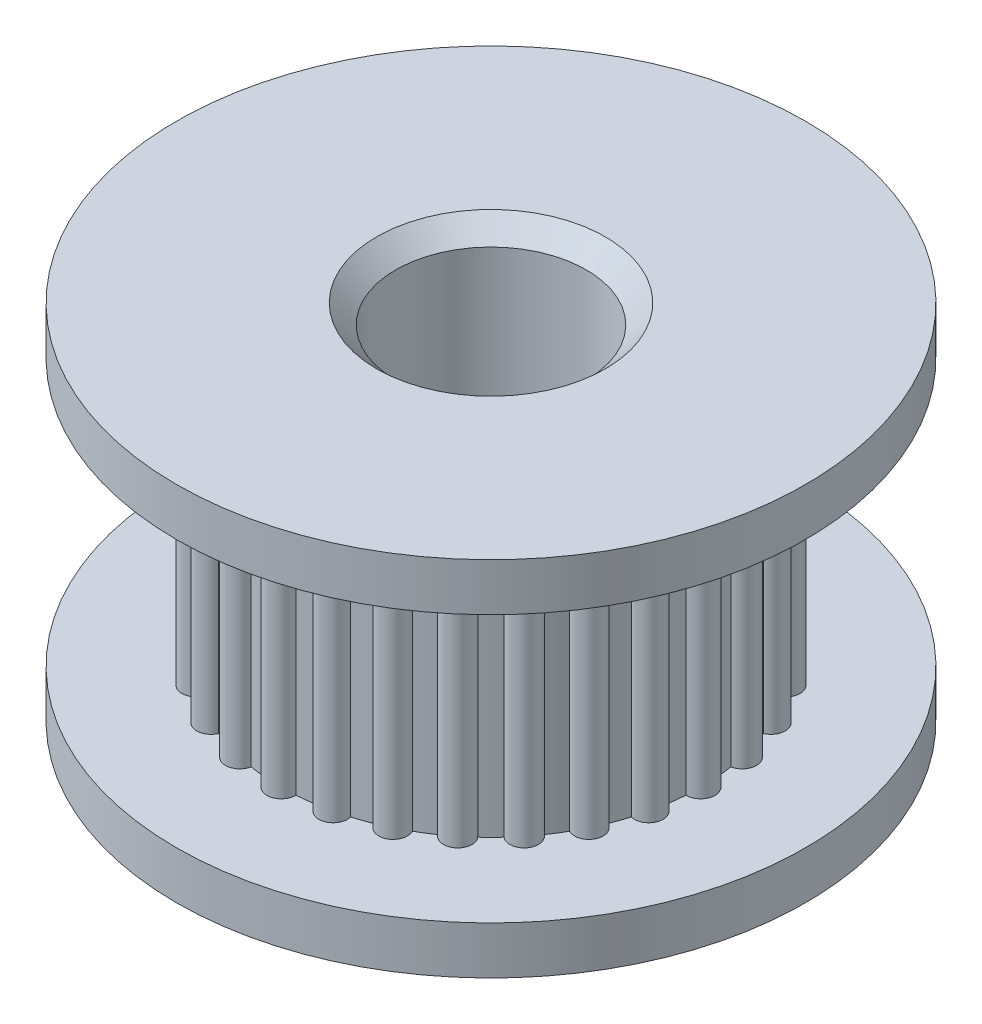
SolidWorks part; units mm, degrees
ref_plane "Front Plane" through (0, 0, 0) normal (0, 0, 1) x (1, 0, 0)
ref_plane "Top Plane" through (0, 0, 0) normal (0, 1, 0) x (1, 0, 0)
ref_plane "Right Plane" through (0, 0, 0) normal (1, 0, 0) x (0, 0, -1)
sketch "Sketch1" plane through (0, 0, 0) normal (0, 1, 0) x (1, 0, 0)
  circle A0 centre (0, 0) radius 8.382
  dimension "D1" = 16.764
extrude "Boss-Extrude1" add sketch "Sketch1" against normal blind 1.27
sketch "Sketch2" plane through (0, 0, 0) normal (0, 1, 0) x (1, 0, 0)
  circle A0 centre (0, 0) radius 5.969 construction
  circle A1 centre (0, 0) radius 5.588 construction
  arc A2 (-5.575, -0.3808) -> (-5.575, 0.3808) centre (-5.588, 0) cw
  circle A3 centre (0, 0) radius 5.588 construction
  arc A4 (-5.52, 0.8693) -> (-5.3505, 1.6118) centre (-5.4479, 1.2434) cw
  arc A6 (-5.1881, 2.0758) -> (-4.8577, 2.762) centre (-5.0346, 2.4245) cw
  arc A8 (-4.5961, 3.1783) -> (-4.1213, 3.7737) centre (-4.3689, 3.4841) cw
  arc A10 (-3.7737, 4.1213) -> (-3.1783, 4.5961) centre (-3.4841, 4.3689) cw
  arc A12 (-2.762, 4.8577) -> (-2.0758, 5.1881) centre (-2.4245, 5.0346) cw
  arc A14 (-1.6118, 5.3505) -> (-0.8693, 5.52) centre (-1.2434, 5.4479) cw
  arc A16 (-0.3808, 5.575) -> (0.3808, 5.575) centre (0, 5.588) cw
  circle A17 centre (0, 0) radius 5.588
  arc A18 (0.8693, 5.52) -> (1.6118, 5.3505) centre (1.2434, 5.4479) cw
  circle A19 centre (0, 0) radius 5.588
  arc A20 (2.0758, 5.1881) -> (2.762, 4.8577) centre (2.4245, 5.0346) cw
  circle A21 centre (0, 0) radius 5.588
  arc A22 (3.1783, 4.5961) -> (3.7737, 4.1213) centre (3.4841, 4.3689) cw
  circle A23 centre (0, 0) radius 5.588
  arc A24 (4.1213, 3.7737) -> (4.5961, 3.1783) centre (4.3689, 3.4841) cw
  circle A25 centre (0, 0) radius 5.588
  arc A26 (4.8577, 2.762) -> (5.1881, 2.0758) centre (5.0346, 2.4245) cw
  circle A27 centre (0, 0) radius 5.588 construction
  arc A28 (5.3505, 1.6118) -> (5.52, 0.8693) centre (5.4479, 1.2434) cw
  circle A29 centre (0, 0) radius 5.588
  arc A30 (5.575, 0.3808) -> (5.575, -0.3808) centre (5.588, 0) cw
  arc A32 (5.52, -0.8693) -> (5.3505, -1.6118) centre (5.4479, -1.2434) cw
  circle A33 centre (0, 0) radius 5.588
  arc A34 (5.1881, -2.0758) -> (4.8577, -2.762) centre (5.0346, -2.4245) cw
  arc A36 (4.5961, -3.1783) -> (4.1213, -3.7737) centre (4.3689, -3.4841) cw
  arc A38 (3.7737, -4.1213) -> (3.1783, -4.5961) centre (3.4841, -4.3689) cw
  circle A39 centre (0, 0) radius 5.588
  arc A40 (2.762, -4.8577) -> (2.0758, -5.1881) centre (2.4245, -5.0346) cw
  arc A42 (1.6118, -5.3505) -> (0.8693, -5.52) centre (1.2434, -5.4479) cw
  circle A43 centre (0, 0) radius 5.588
  arc A44 (0.3808, -5.575) -> (-0.3808, -5.575) centre (0, -5.588) cw
  arc A46 (-0.8693, -5.52) -> (-1.6118, -5.3505) centre (-1.2434, -5.4479) cw
  circle A47 centre (0, 0) radius 5.588
  arc A48 (-2.0758, -5.1881) -> (-2.762, -4.8577) centre (-2.4245, -5.0346) cw
  circle A49 centre (0, 0) radius 5.588
  arc A50 (-3.1783, -4.5961) -> (-3.7737, -4.1213) centre (-3.4841, -4.3689) cw
  circle A51 centre (0, 0) radius 5.588
  arc A52 (-4.1213, -3.7737) -> (-4.5961, -3.1783) centre (-4.3689, -3.4841) cw
  circle A53 centre (0, 0) radius 5.588
  arc A54 (-4.8577, -2.762) -> (-5.1881, -2.0758) centre (-5.0346, -2.4245) cw
  circle A55 centre (0, 0) radius 5.588
  arc A56 (-5.3505, -1.6118) -> (-5.52, -0.8693) centre (-5.4479, -1.2434) cw
  circle A57 centre (0, 0) radius 5.588 [skipped]
  circle A58 centre (0, 0) radius 5.588 [skipped]
  circle A59 centre (0, 0) radius 5.588 [skipped]
  circle A60 centre (0, 0) radius 5.588 [skipped]
  circle A61 centre (0, 0) radius 5.588 [skipped]
  circle A62 centre (0, 0) radius 5.588 [skipped]
  circle A63 centre (0, 0) radius 5.588 [skipped]
  circle A64 centre (0, 0) radius 5.588 [skipped]
  circle A65 centre (0, 0) radius 5.588 [skipped]
  circle A66 centre (0, 0) radius 5.588 [skipped]
  circle A67 centre (0, 0) radius 5.588 [skipped]
  point P117 (0, 0)
  dimension "D1" = 11.938
  dimension "D2" = 0.381
  dimension "D3" = 28
extrude "Boss-Extrude2" add sketch "Sketch2" along normal blind 7.112 contours A17 A8 | A17 A6 | A17 A4 | A17 A2 | A56 A55 | A54 A53 | A52 A51 | A48 A47 | A46 A43 | A40 A39 | A38 A33 | A36 A33 | A34 A33 | A30 A29 | A28 A25 | A26 A25 | A24 A23 | A22 A21 | A20 A19 | A18 A17 | A17 A16 | A17 A14 | A17 A12 | A17 A10 | A50 A49 | A44 A43 | A42 A39 | A32 A29 | A17 A55 A53 A51 A49 A47 A43 A39 A33 A29 A25 A23 A21 A19
sketch "Sketch3" plane through (0, 7.112, 0) normal (0, 1, 0) x (1, 0, 0)
  circle A0 centre (0, 0) radius 8.382 construction
  circle A1 centre (0, 0) radius 8.382
extrude "Boss-Extrude3" add sketch "Sketch3" along normal blind 1.27
sketch "Sketch4" plane through (0, -1.27, 0) normal (0, -1, 0) x (1, 0, 0)
  circle A0 centre (0, 0) radius 2.54
  point P3 (0, 0)
  dimension "D1" = 5.08
extrude "Cut-Extrude1" cut sketch "Sketch4" against normal through all both and the other way through all
chamfer "Chamfer1" distance 0.508 angle 45 2 edges at (0, 8.382, -2.54) (0, -1.27, 2.54)
